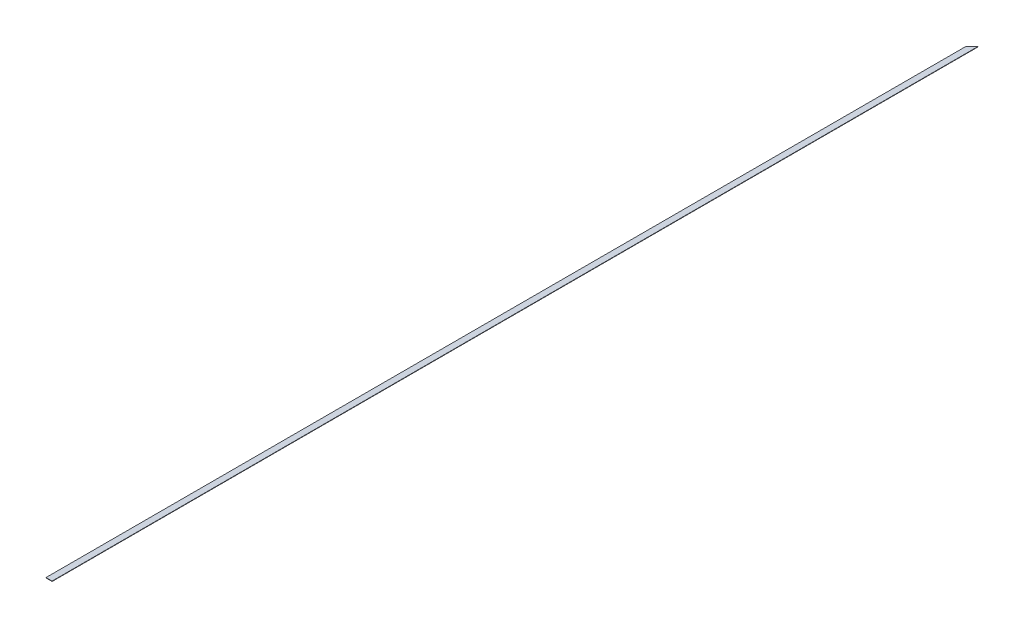
SolidWorks part; units mm, degrees
ref_plane "Front Plane" through (0, 0, 0) normal (0, 0, 1) x (1, 0, 0)
ref_plane "Top Plane" through (0, 0, 0) normal (0, 1, 0) x (1, 0, 0)
ref_plane "Right Plane" through (0, 0, 0) normal (1, 0, 0) x (0, 0, -1)
sketch "Sketch1" plane through (0, 0, 0) normal (0, 1, 0) x (1, 0, 0)
  line L1 (-25.3159, 3810.0421) -> (25.4841, 3860.8421)
  line L2 (-25.3159, 3810.0421) -> (-25.3159, -3835.3579)
  line L3 (-25.3159, -3835.3579) -> (25.4841, -3835.3579)
  line L4 (25.4841, 3860.8421) -> (25.4841, -3835.3579)
  line L5 (-25.3159, 3810.0421) -> (25.4841, -3835.3579) construction
  line L6 (-25.3159, -3835.3579) -> (25.4841, 3860.8421) construction
  point P0 (0, 0)
  dimension "D1" = 50.8
  dimension "D2" = 7696.2
  dimension "D3" = 45
extrude "Boss-Extrude1" add sketch "Sketch1" along normal blind 3.175
